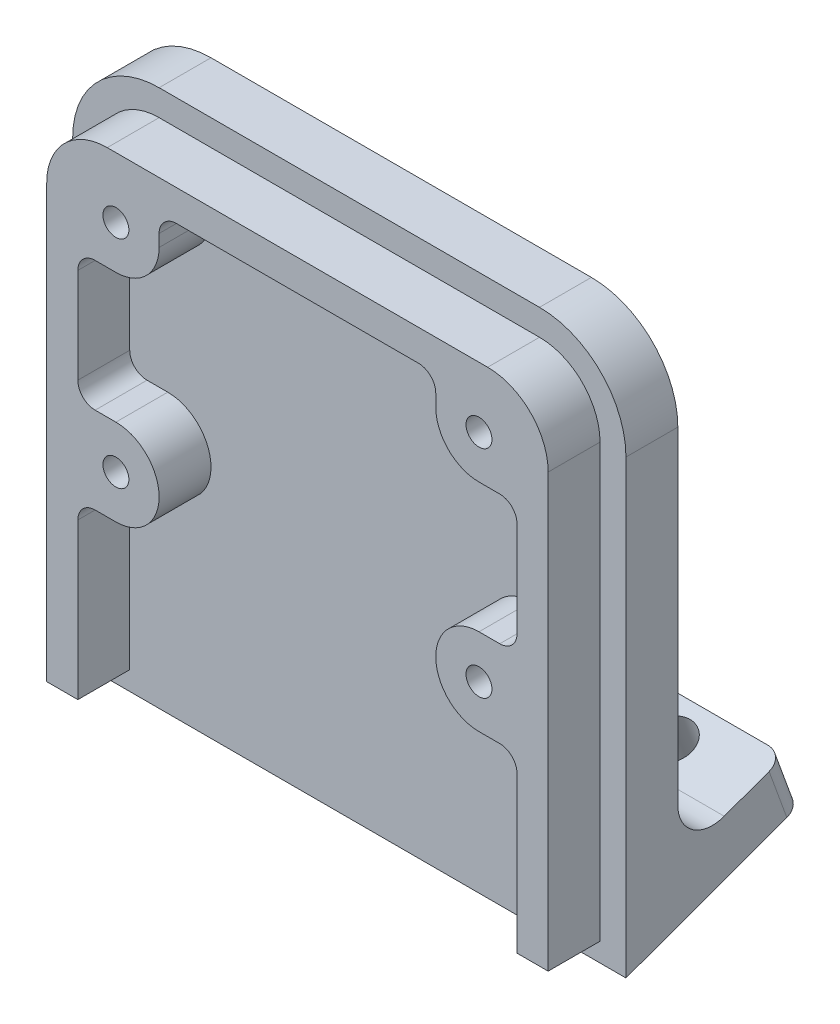
SolidWorks part; units mm, degrees
ref_plane "Front" through (0, 0, 0) normal (0, 0, 1) x (1, 0, 0)
ref_plane "Top" through (0, 0, 0) normal (0, 1, 0) x (1, 0, 0)
ref_plane "Right" through (0, 0, 0) normal (1, 0, 0) x (0, 0, -1)
sketch "Sketch1" plane through (0, 0, 0) normal (0, 0, 1) x (1, 0, 0)
  line L1 (0, 0) -> (32, 0)
  line L2 (0, 0) -> (0, 30)
  line L3 (0, 30) -> (32, 30)
  line L4 (32, 0) -> (32, 30)
  dimension "D1" = 32
  dimension "D2" = 30
extrude "Boss-Extrude1" add sketch "Sketch1" along normal blind 3
sketch "Sketch2" plane through (0, 0, 3) normal (0, 0, 1) x (1, 0, 0)
  line L0 (0, 0) -> (32, 0) construction
  line L1 (1.5, 0) -> (3.3, 0)
  line L2 (1.5, 0) -> (1.5, 28.5)
  line L3 (1.5, 28.5) -> (30.5, 28.5)
  line L4 (30.5, 0) -> (30.5, 28.5)
  line L5 (0, 30) -> (0, 0) construction
  line L6 (32, 30) -> (0, 30) construction
  line L7 (32, 0) -> (32, 30) construction
  line L8 (3.3, 0) -> (3.3, 10)
  line L10 (28.7, 22.5) -> (28.7, 15)
  line L11 (28.7, 0) -> (30.5, 0)
  line L12 (16, 30) -> (16, 0) construction
  line L13 (8, 25) -> (8, 26.7)
  line L14 (26.5, 12.5) -> (5.5, 12.5) construction
  line L15 (26.5, 12.5) -> (26.5, 25) construction
  line L16 (26.5, 25) -> (5.5, 25) construction
  line L17 (5.5, 12.5) -> (5.5, 25) construction
  line L18 (26.5, 12.5) -> (5.5, 25) construction
  line L19 (26.5, 25) -> (5.5, 12.5) construction
  line L20 (5.5, 22.5) -> (3.3, 22.5)
  line L21 (5.5, 15) -> (3.3, 15)
  line L22 (5.5, 10) -> (3.3, 10)
  line L23 (26.5, 10) -> (28.7, 10)
  line L24 (24, 25) -> (24, 26.7)
  line L25 (26.5, 22.5) -> (28.7, 22.5)
  line L26 (8, 26.7) -> (24, 26.7)
  line L28 (28.7, 10) -> (28.7, 0)
  line L29 (26.5, 15) -> (28.7, 15)
  line L30 (3.3, 15) -> (3.3, 22.5)
  arc A0 (5.5, 22.5) -> (8, 25) centre (5.5, 25) ccw
  arc A1 (24, 25) -> (26.5, 22.5) centre (26.5, 25) ccw
  arc A2 (26.5, 15) -> (26.5, 10) centre (26.5, 12.5) ccw
  arc A3 (5.5, 10) -> (5.5, 15) centre (5.5, 12.5) ccw
  point P18 (16, 18.75)
  dimension "D7" = 5
  dimension "D1" = 1.5
  dimension "D2" = 1.5
  dimension "D3" = 1.5
  dimension "D4" = 1.8
  dimension "D6" = 1.8
  dimension "D8" = 21
  dimension "D9" = 12.5
  dimension "D10" = 5
  dimension "D5" = 1.8
extrude "Boss-Extrude2" add sketch "Sketch2" along normal blind 3
hole_wizard "Ø1.5mm Clearance Dowel Hole1" positions "3DSketch1" profile "Sketch3" hole size "Ø1.5" standard "ISO"
sketch3d "3DSketch1"
  line L0 (5.5, 25, 6) -> (5.5, 25, 3) construction
  line L1 (26.5, 25, 6) -> (26.5, 25, 3) construction
  line L2 (5.5, 12.5, 6) -> (5.5, 12.5, 3) construction
  line L3 (26.5, 12.5, 6) -> (26.5, 12.5, 3) construction
  point P0 (5.5, 25, 6)
  point P4 (26.5, 25, 6)
  point P12 (26.5, 12.5, 6)
  point P18 (5.5, 12.5, 6)
sketch "Sketch3" plane through (5.5, 25, 6) normal (1, 0, 0) x (0, -1, 0)
  line L0 (0, 0) -> (0, 5.4506)
  line L1 (0, 5.4506) -> (0.75, 5)
  line L2 (0.75, 5) -> (0.75, 0)
  line L5 (0.75, 0) -> (0, 0)
  line L10 (0, 5.4506) -> (-0.75, 5) construction
  line L11 (0, -6.35) -> (0, 107.95) construction
  dimension "Hole Dia." = 1.5
  dimension "Hole Depth" = 5
  dimension "Drill Angle" = 118
fillet "Fillet1" radius 5 2 edges at (32, 30, 1.5) (0, 30, 1.5)
fillet "Fillet2" radius 3.5 2 edges at (30.5, 28.5, 4.5) (1.5, 28.5, 4.5)
sketch "Sketch5" plane through (0, 0, 0) normal (-1, 0, 0) x (0, 0, 1)
  line L1 (0, 0) -> (-7.2439, 2.6365)
  line L2 (-7.2439, 2.6365) -> (-6.2178, 5.4556)
  line L3 (-6.2178, 5.4556) -> (0, 3.1925)
  line L7 (0, 25) -> (0, 0) construction
  line L8 (0, 3.1925) -> (0, 0)
  line L9 (3, 0) -> (0, 0) construction
  line L12 (-9.296, -3.0016) -> (-7.2439, 2.6365) construction
  dimension "D1" = 20
  dimension "D4" = 3
extrude "Boss-Extrude4" add sketch "Sketch5" against normal up to surface (32 mm away) up to face at (32, 12.5, 1.5)
sketch "Sketch7" plane through (0, 0, 0) normal (-1, 0, 0) x (0, 0, 1)
  line L0 (0, 0) -> (3, -1.0919)
  line L1 (3, -1.0919) -> (3, 0)
  line L2 (3, 0) -> (0, 0)
  line L3 (-7.2439, 2.6365) -> (0, 0) construction
  line L4 (3, 25) -> (3, 0) construction
extrude "Boss-Extrude5" add sketch "Sketch7" against normal up to surface (32 mm away) up to face at (32, 8.755, -1.0659)
sketch "Sketch8" plane through (0, 2.8191, 1.0261) normal (0, 0.9397, 0.342) x (1, 0, 0)
  line L0 (16, 1.0919) -> (16, 7.7087) construction
  line L1 (32, 1.0919) -> (0, 1.0919) construction
  line L2 (32, 7.7087) -> (0, 7.7087) construction
  line L4 (27.1894, 0.7087) -> (4.8106, 0.7087) construction
  line L5 (27.1894, 0.7087) -> (27.1894, 5.7087) construction
  line L6 (27.1894, 5.7087) -> (4.8106, 5.7087) construction
  line L7 (4.8106, 0.7087) -> (4.8106, 5.7087) construction
  line L8 (27.1894, 0.7087) -> (4.8106, 5.7087) construction
  line L9 (27.1894, 5.7087) -> (4.8106, 0.7087) construction
  circle A0 centre (4.8106, 0.7087) radius 1.25 construction
  circle A1 centre (4.8106, 5.7087) radius 1.25
  circle A2 centre (27.1894, 5.7087) radius 1.25
  circle A3 centre (27.1894, 0.7087) radius 1.25 construction
  point P6 (16, 3.2087)
  dimension "D1" = 2.5
  dimension "D2" = 22.3788
  dimension "D3" = 2
  dimension "D4" = 5
extrude "Cut-Extrude1" cut sketch "Sketch8" against normal through all
fillet "Fillet3" radius 1 8 edges at (28.7, 15, 4.5) (28.7, 10, 4.5) (28.7, 22.5, 4.5) (24, 26.7, 4.5) (8, 26.7, 4.5) (3.3, 15, 4.5) (3.3, 22.5, 4.5) (3.3, 10, 4.5)
fillet "Fillet4" radius 2 1 edges at (16, 3.1925, 0)
fillet "Fillet5" radius 1 2 edges at (0, 4.0461, -6.7308) (32, 4.0461, -6.7308)
equation "\"D5@Sketch2\"=\"D4@Sketch2\""
